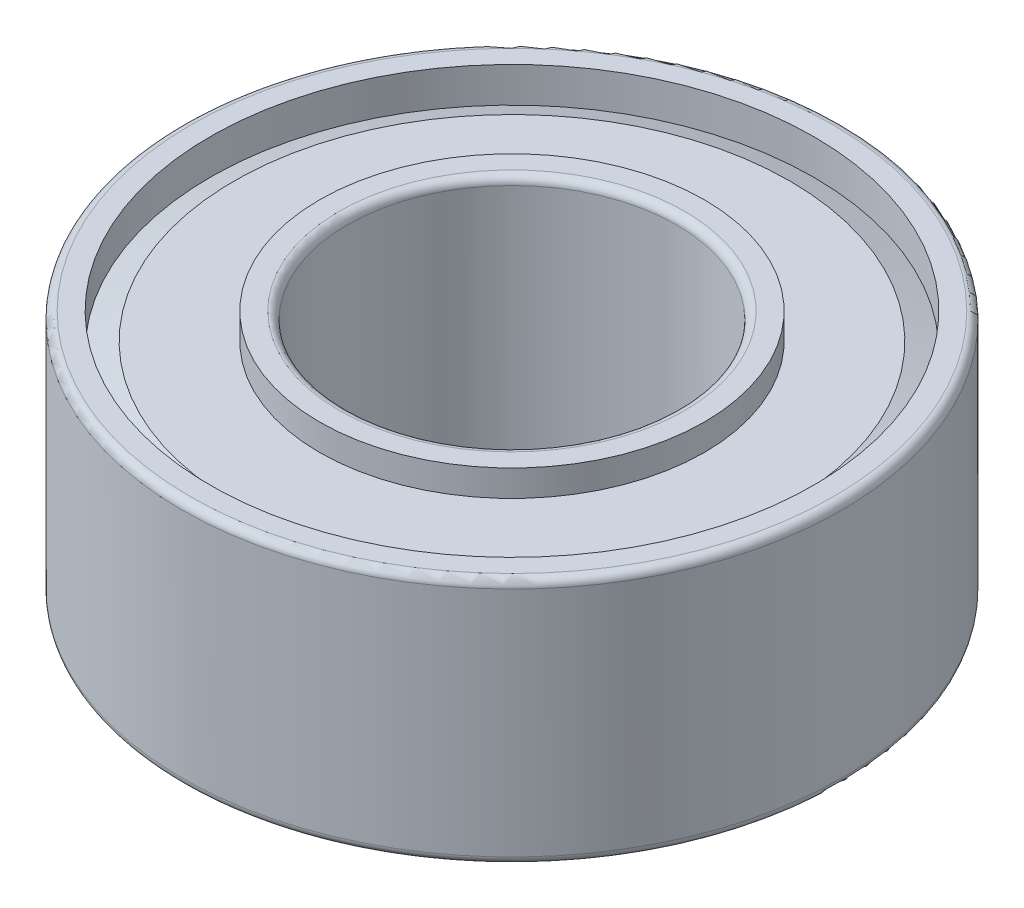
SolidWorks part; units mm, degrees
ref_plane "Front Plane" through (0, 0, 0) normal (0, 0, 1) x (1, 0, 0)
ref_plane "Top Plane" through (0, 0, 0) normal (0, 1, 0) x (1, 0, 0)
ref_plane "Right Plane" through (0, 0, 0) normal (1, 0, 0) x (0, 0, -1)
sketch "Sketch1" plane through (0, 0, 0) normal (0, 0, 1) x (1, 0, 0)
  line L0 (0, 0) -> (0, 92.0905) construction
  line L1 (6.35, 2.3876) -> (-9.8986, 2.3876) construction
  line L2 (3.175, 4.7752) -> (6.35, 4.7752)
  line L3 (3.175, 4.7752) -> (3.175, 0)
  line L4 (3.175, 0) -> (6.35, 0)
  line L5 (6.35, 4.7752) -> (6.35, 0)
  line L6 (4.7625, 4.7752) -> (4.7625, -3.8915) construction
  circle A0 centre (4.7625, 2.3876) radius 1.2065
  dimension "D4" = 2.413
  dimension "D1" = 6.35
  dimension "D2" = 12.7
  dimension "D3" = 4.7752
revolve "Revolve1" add sketch "Sketch1" angle 360 about L0
sketch "Sketch2" plane through (0, 0, 0) normal (0, 0, 1) x (1, 0, 0)
  line L0 (3.7084, 4.7752) -> (3.7084, 4.2672)
  line L1 (6.35, 4.7752) -> (-6.35, 4.7752) construction
  line L2 (3.7084, 4.2672) -> (5.3531, 4.2672)
  line L3 (5.3531, 4.2672) -> (5.8166, 4.0963)
  line L4 (5.8166, 4.0963) -> (5.8166, 4.7752)
  line L5 (5.8166, 4.7752) -> (3.7084, 4.7752)
  line L6 (0, 0) -> (0, 7.2736) construction
  dimension "D1" = 0.508
  dimension "D2" = 1.6447
  dimension "D3" = 0.6789
  dimension "D4" = 2.1082
  dimension "D5" = 3.7084
revolve "Cut-Revolve1" cut sketch "Sketch2" angle 360 about L6
ref_plane "Plane1" through (0, 2.3876, 0) normal (0, -1, 0) x (1, 0, 0)
mirror "Mirror1" about plane through (0, 2.3876, 0) normal (0, -1, 0) of "Cut-Revolve1"
fillet "Fillet1" radius 0.1524 4 edges at (0, 4.7752, -3.175) (0, 4.7752, -6.35) (0, 0, -6.35) (0, 0, -3.175)
